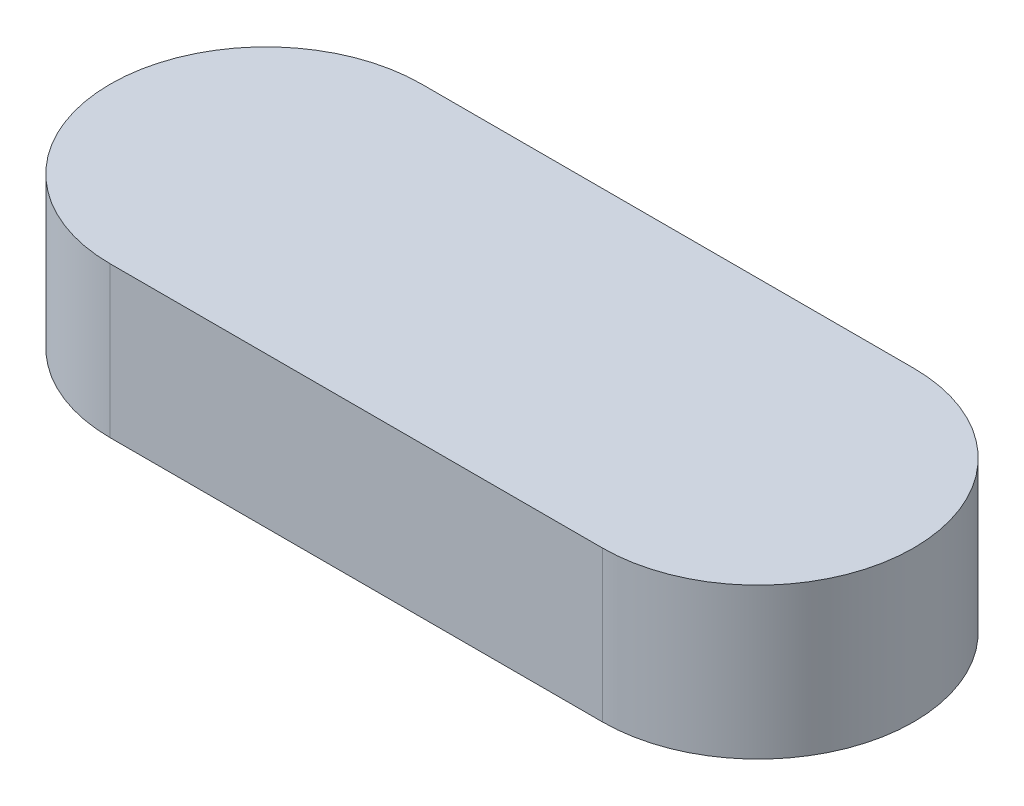
SolidWorks part; units mm, degrees
ref_plane "Front Plane" through (0, 0, 0) normal (0, 0, 1) x (1, 0, 0)
ref_plane "Top Plane" through (0, 0, 0) normal (0, 1, 0) x (1, 0, 0)
ref_plane "Right Plane" through (0, 0, 0) normal (1, 0, 0) x (0, 0, -1)
sketch "Sketch2" plane through (0, 0, 0) normal (0, 1, 0) x (1, 0, 0)
  line L0 (-9.5421, 0) -> (14.9579, 0) construction
  line L1 (-9.5421, 7.75) -> (14.9579, 7.75)
  line L2 (-9.5421, -7.75) -> (14.9579, -7.75)
  arc A0 (-9.5421, 7.75) -> (-9.5421, -7.75) centre (-9.5421, 0) ccw
  arc A1 (14.9579, -7.75) -> (14.9579, 7.75) centre (14.9579, 0) ccw
  point P3 (2.7079, 0)
  dimension "D2" = 7.75
  dimension "D1" = 24.5
extrude "Boss-Extrude1" add sketch "Sketch2" along normal blind 7.5
